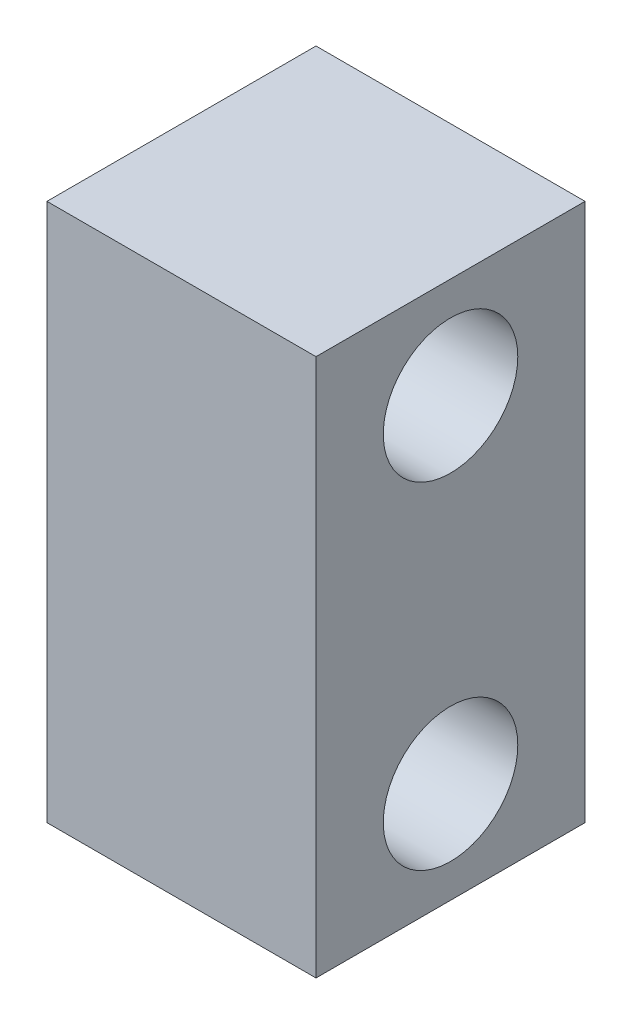
SolidWorks part; units mm, degrees
ref_plane "Front Plane" through (0, 0, 0) normal (0, 0, 1) x (1, 0, 0)
ref_plane "Top Plane" through (0, 0, 0) normal (0, 1, 0) x (1, 0, 0)
ref_plane "Right Plane" through (0, 0, 0) normal (1, 0, 0) x (0, 0, -1)
sketch "Sketch1" plane through (0, 0, 0) normal (0, 0, 1) x (1, 0, 0)
  line L1 (0, 0) -> (50.8, 0)
  line L2 (0, 0) -> (0, 101.6)
  line L3 (0, 101.6) -> (50.8, 101.6)
  line L4 (50.8, 0) -> (50.8, 101.6)
  dimension "D1" = 101.6
  dimension "D2" = 50.8
extrude "Boss-Extrude1" add sketch "Sketch1" along normal blind 50.8
sketch "Sketch2" plane through (50.8, 0, 0) normal (1, 0, 0) x (0, 0, -1)
  line L0 (-50.8, 0) -> (-50.8, 101.6) construction
  line L1 (-50.8, 101.6) -> (0, 101.6) construction
  line L2 (-50.8, 0) -> (0, 0) construction
  circle A0 centre (-25.4, 82.55) radius 12.7
  circle A1 centre (-25.4, 19.05) radius 12.7
  dimension "D1" = 25.4
  dimension "D2" = 25.4
  dimension "D3" = 25.4
  dimension "D4" = 25.4
  dimension "D5" = 19.05
  dimension "D6" = 19.05
extrude "Cut-Extrude1" cut sketch "Sketch2" against normal through all
